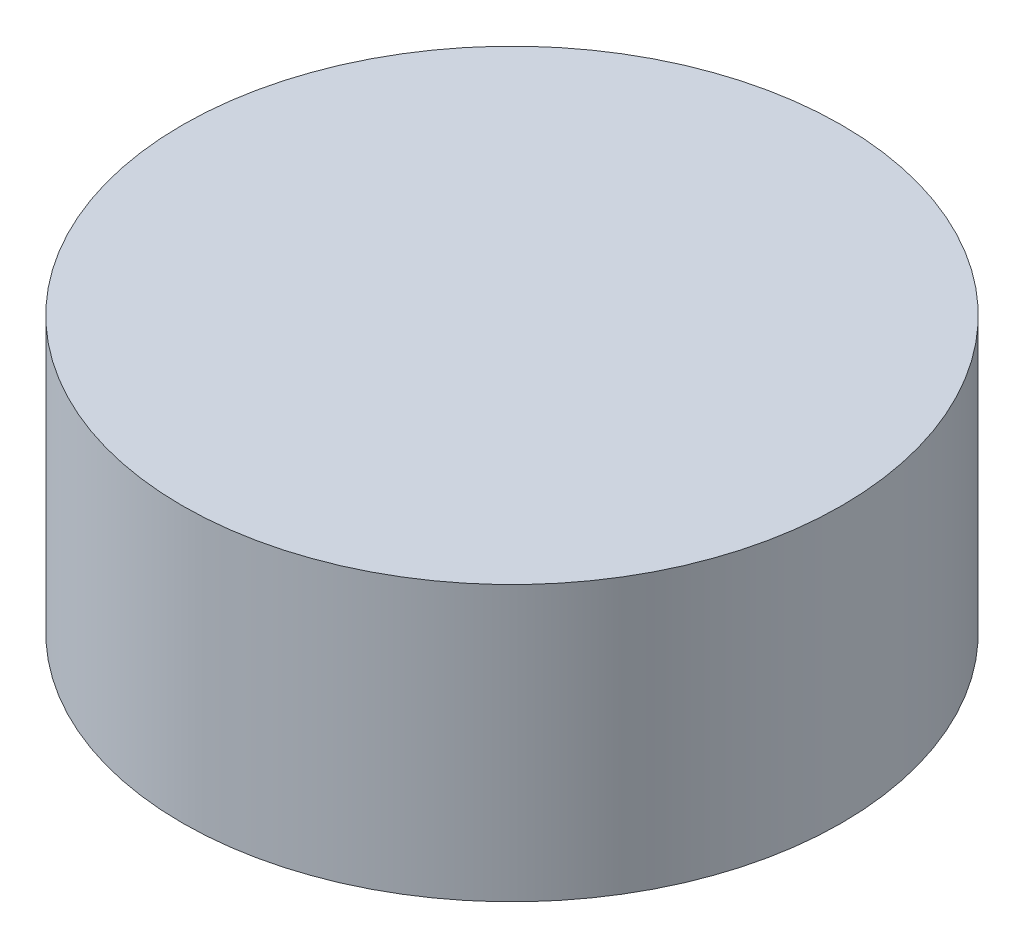
SolidWorks part; units mm, degrees
ref_plane "Front Plane" through (0, 0, 0) normal (0, 0, 1) x (1, 0, 0)
ref_plane "Top Plane" through (0, 0, 0) normal (0, 1, 0) x (1, 0, 0)
ref_plane "Right Plane" through (0, 0, 0) normal (1, 0, 0) x (0, 0, -1)
sketch "Sketch1" plane through (0, 0, 0) normal (0, 1, 0) x (1, 0, 0)
  circle A0 centre (0, 0) radius 30
extrude "Boss-Extrude1" add sketch "Sketch1" along normal blind 25 contours A0
